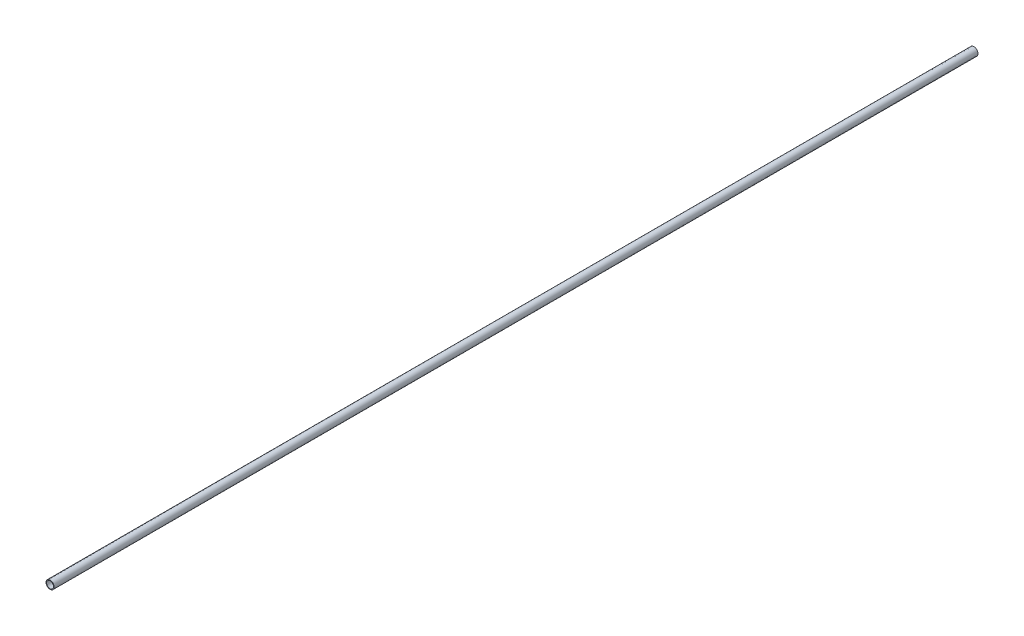
SolidWorks part; units mm, degrees
ref_plane "Front" through (0, 0, 0) normal (0, 0, 1) x (1, 0, 0)
ref_plane "Top" through (0, 0, 0) normal (0, 1, 0) x (1, 0, 0)
ref_plane "Side" through (0, 0, 0) normal (1, 0, 0) x (0, 0, -1)
sketch "PipeSketch" plane through (0, 0, 0) normal (0, 0, 1) x (1, 0, 0)
  circle A0 centre (0, 0) radius 24.13
  circle A1 centre (0, 0) radius 20.447
  dimension "OuterDiameter" = 48.26
  dimension "InnerDiameter" = 40.894
extrude "Extrusion" add sketch "PipeSketch" along normal blind 5486.4
sketch "FilterSketch" plane through (0, 0, 0) normal (0, 0, 1) x (1, 0, 0)
  circle A0 centre (0, 0) radius 19.05 construction
  dimension "NominalDiameter" = 38.1
